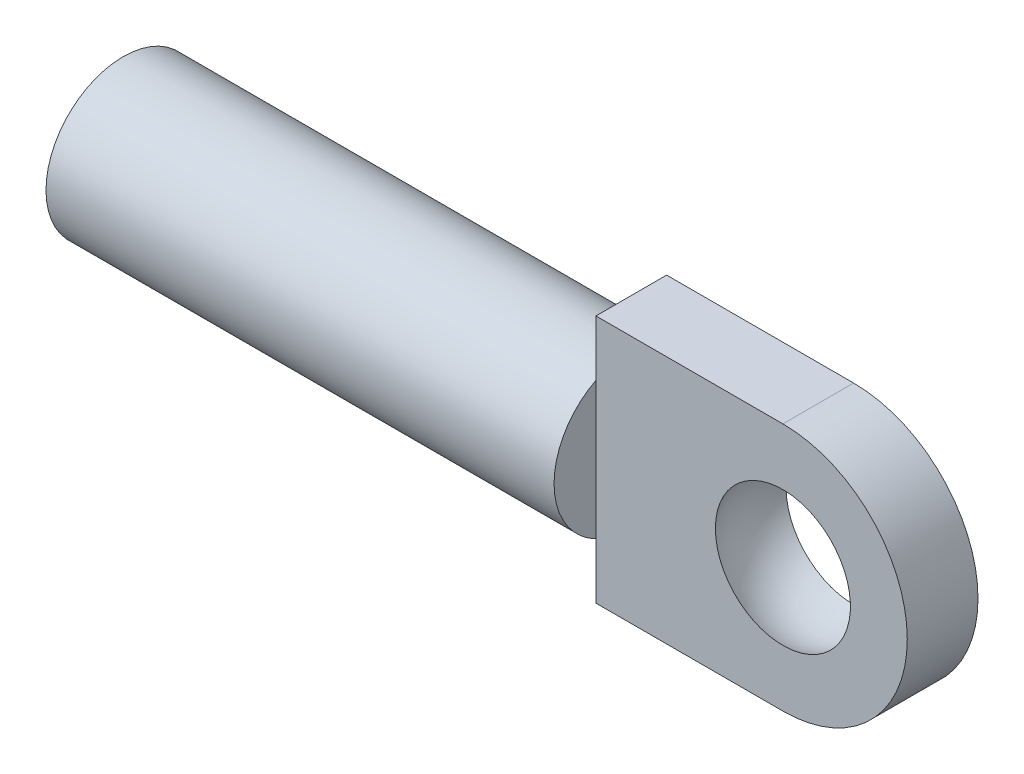
SolidWorks part; units mm, degrees
ref_plane "Front Plane" through (0, 0, 0) normal (0, 0, 1) x (1, 0, 0)
ref_plane "Top Plane" through (0, 0, 0) normal (0, 1, 0) x (1, 0, 0)
ref_plane "Right Plane" through (0, 0, 0) normal (1, 0, 0) x (0, 0, -1)
sketch "Sketch1" plane through (0, 0, 0) normal (0, 0, 1) x (1, 0, 0)
  line L0 (0, 3.8862) -> (-5.842, 3.8862)
  line L1 (0, -3.8862) -> (-5.842, -3.8862)
  line L2 (-5.842, 3.8862) -> (-5.842, -3.8862)
  arc A0 (0, 3.8862) -> (0, -3.8862) centre (0, 0) cw
extrude "Extrude1" add sketch "Sketch1" along normal blind 1.1049 and the other way blind 1.1049
sketch "Sketch2" plane through (-5.842, 0, 0) normal (-1, 0, 0) x (0, 0, 1)
  line L0 (-1.1049, 0) -> (1.1049, 0) construction
  line L1 (-1.1049, 3.8862) -> (-1.1049, -3.8862) construction
  line L2 (1.1049, 3.8862) -> (1.1049, -3.8862) construction
  circle A0 centre (0, 0) radius 2.413
extrude "Extrude2" add sketch "Sketch2" along normal blind 15.875
sketch "Sketch3" plane through (-21.717, 0, 0) normal (-1, 0, 0) x (0, 0, 1)
  circle A0 centre (0, 0) radius 1.2065
extrude "Extrude3" cut sketch "Sketch3" against normal blind 14.859
ref_plane "Plane1" through (0, 0, 0) normal (0, 0, 1) x (1, 0, 0)
sketch "Sketch6" plane through (0, 0, 0) normal (0, 0, 1) x (1, 0, 0)
  line L0 (0, -2.3813) -> (0, 2.3813)
  arc A0 (0, -2.3813) -> (0, 2.3813) centre (0, 0) cw
revolve "Cut-Revolve1" cut sketch "Sketch6" angle 360 about L0
